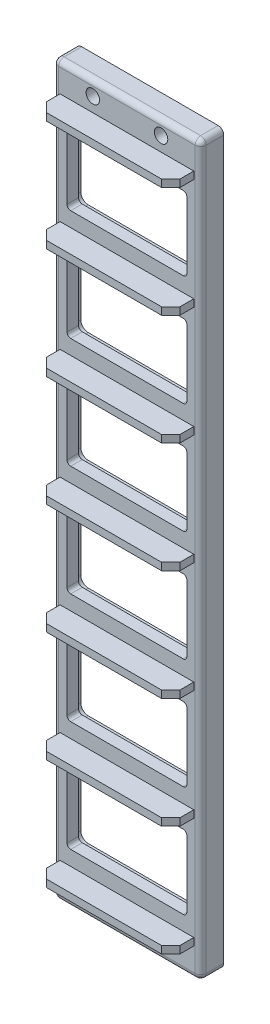
SolidWorks part; units mm, degrees
ref_plane "Front Plane" through (0, 0, 0) normal (0, 0, 1) x (1, 0, 0)
ref_plane "Top Plane" through (0, 0, 0) normal (0, 1, 0) x (1, 0, 0)
ref_plane "Right Plane" through (0, 0, 0) normal (1, 0, 0) x (0, 0, -1)
sketch "Sketch2" plane through (0, 0, 0) normal (0, 0, 1) x (1, 0, 0)
  line L0 (-101.9175, -92.329) -> (-83.5025, -92.329) construction
  line L7 (-101.9175, -107.569) -> (-83.5025, -107.569) construction
  line L14 (-101.9175, -108.077) -> (-83.5025, -108.077)
  line L21 (-101.9175, -107.061) -> (-83.5025, -107.061)
  line L34 (-101.9175, -108.077) -> (-101.9175, -107.061)
  line L35 (-83.5025, -108.077) -> (-83.5025, -107.061)
  arc A0 (-100.6475, -91.059) -> (-100.6475, -93.599) centre (-100.6475, -92.329) ccw construction
  arc A1 (-84.7725, -93.599) -> (-84.7725, -91.059) centre (-84.7725, -92.329) ccw construction
  dimension "D1" = 15.24
  dimension "D4" = 0.508
  dimension "D5" = 0.508
  dimension "D3" = 2
extrude "Boss-Extrude1" add sketch "Sketch2" along normal blind 6.35
chamfer "Chamfer1" distance 1.27 angle 45 2 edges at (-101.9175, -107.569, 6.35) (-83.5025, -107.569, 6.35)
pattern_linear "LPattern2" count 7 spacing 15.24 along (0, 1, 0) of bodies 107
sketch "Sketch3" plane through (0, 0, 0) normal (0, 0, 1) x (1, 0, 0)
  line L0 (-102.87, -112.014) -> (-82.55, -112.014) construction
  line L1 (-82.55, -112.014) -> (-82.55, -11.684) construction
  line L2 (-82.55, -11.684) -> (-102.87, -11.684) construction
  line L3 (-102.87, -11.684) -> (-102.87, -112.014) construction
  line L4 (-84.455, -94.869) -> (-100.965, -94.869) construction
  line L5 (-100.965, -94.869) -> (-100.965, -105.029) construction
  line L6 (-100.965, -105.029) -> (-84.455, -105.029) construction
  line L7 (-84.455, -105.029) -> (-84.455, -94.869) construction
  line L8 (-84.455, -89.789) -> (-84.455, -79.629) construction
  line L9 (-84.455, -79.629) -> (-100.965, -79.629) construction
  line L10 (-100.965, -79.629) -> (-100.965, -89.789) construction
  line L11 (-100.965, -89.789) -> (-84.455, -89.789) construction
  line L12 (-84.455, -74.549) -> (-84.455, -64.389) construction
  line L13 (-84.455, -64.389) -> (-100.965, -64.389) construction
  line L14 (-100.965, -64.389) -> (-100.965, -74.549) construction
  line L15 (-100.965, -74.549) -> (-84.455, -74.549) construction
  line L16 (-84.455, -59.309) -> (-84.455, -49.149) construction
  line L17 (-84.455, -49.149) -> (-100.965, -49.149) construction
  line L18 (-100.965, -49.149) -> (-100.965, -59.309) construction
  line L19 (-100.965, -59.309) -> (-84.455, -59.309) construction
  line L20 (-84.455, -44.069) -> (-84.455, -33.909) construction
  line L21 (-84.455, -33.909) -> (-100.965, -33.909) construction
  line L22 (-100.965, -33.909) -> (-100.965, -44.069) construction
  line L23 (-100.965, -44.069) -> (-84.455, -44.069) construction
  line L24 (-84.455, -28.829) -> (-84.455, -18.669) construction
  line L25 (-84.455, -18.669) -> (-100.965, -18.669) construction
  line L26 (-100.965, -18.669) -> (-100.965, -28.829) construction
  line L27 (-100.965, -28.829) -> (-84.455, -28.829) construction
  line L28 (-102.87, -112.014) -> (-82.55, -112.014)
  line L29 (-82.55, -112.014) -> (-82.55, -11.684)
  line L30 (-82.55, -11.684) -> (-102.87, -11.684)
  line L31 (-102.87, -11.684) -> (-102.87, -112.014)
  line L32 (-84.455, -94.869) -> (-100.965, -94.869)
  line L33 (-100.965, -94.869) -> (-100.965, -105.029)
  line L34 (-100.965, -105.029) -> (-84.455, -105.029)
  line L35 (-84.455, -105.029) -> (-84.455, -94.869)
  line L36 (-84.455, -89.789) -> (-84.455, -79.629)
  line L37 (-84.455, -79.629) -> (-100.965, -79.629)
  line L38 (-100.965, -79.629) -> (-100.965, -89.789)
  line L39 (-100.965, -89.789) -> (-84.455, -89.789)
  line L40 (-84.455, -74.549) -> (-84.455, -64.389)
  line L41 (-84.455, -64.389) -> (-100.965, -64.389)
  line L42 (-100.965, -64.389) -> (-100.965, -74.549)
  line L43 (-100.965, -74.549) -> (-84.455, -74.549)
  line L44 (-84.455, -59.309) -> (-84.455, -49.149)
  line L45 (-84.455, -49.149) -> (-100.965, -49.149)
  line L46 (-100.965, -49.149) -> (-100.965, -59.309)
  line L47 (-100.965, -59.309) -> (-84.455, -59.309)
  line L48 (-84.455, -44.069) -> (-84.455, -33.909)
  line L49 (-84.455, -33.909) -> (-100.965, -33.909)
  line L50 (-100.965, -33.909) -> (-100.965, -44.069)
  line L51 (-100.965, -44.069) -> (-84.455, -44.069)
  line L52 (-84.455, -28.829) -> (-84.455, -18.669)
  line L53 (-84.455, -18.669) -> (-100.965, -18.669)
  line L54 (-100.965, -18.669) -> (-100.965, -28.829)
  line L55 (-100.965, -28.829) -> (-84.455, -28.829)
extrude "Boss-Extrude2" add sketch "Sketch3" along normal blind 3.175
fillet "Fillet1" radius 0.762 8 edges at (-102.87, -112.014, 1.5875) (-92.71, -112.014, 3.175) (-82.55, -112.014, 1.5875) (-92.71, -11.684, 3.175) (-102.87, -61.849, 3.175) (-82.55, -61.849, 3.175) (-102.87, -11.684, 1.5875) (-82.55, -11.684, 1.5875)
hole_wizard "#0 Clearance Hole1" positions "Sketch8" profile "Sketch7" hole size "#0" standard "ANSI Inch" end condition through all
sketch "Sketch8" plane through (0, 0, 3.175) normal (0, 0, 1) x (1, 0, 0)
  line L0 (-92.71, -15.621) -> (-92.71, -11.684) construction
  line L1 (-101.9175, -15.621) -> (-83.5025, -15.621) construction
  line L2 (-102.108, -11.684) -> (-83.312, -11.684) construction
  line L4 (-92.71, -13.6525) -> (-102.108, -13.6525) construction
  line L5 (-102.108, -12.446) -> (-102.108, -111.252) construction
  line L6 (-102.87, -61.849) -> (-82.55, -61.849) construction
  line L7 (-102.87, -111.252) -> (-102.87, -12.446) construction
  line L8 (-82.55, -12.446) -> (-82.55, -111.252) construction
  point P19 (-97.409, -13.6525)
  point P21 (-88.011, -13.6525)
  point P30 (-97.409, -110.0455)
  point P31 (-88.011, -110.0455)
sketch "Sketch7" plane through (-97.409, -13.6525, 3.175) normal (1, 0, 0) x (0, -1, 0)
  line L0 (0, 0) -> (0, 3.175)
  line L1 (0, 3.175) -> (0.9271, 3.175)
  line L2 (0.9271, 3.175) -> (0.9271, 0)
  line L5 (0.9271, 0) -> (0, 0)
  line L11 (0, -6.35) -> (0, 107.95) construction
  dimension "Thru Hole Dia." = 1.8542
  dimension "Thru Hole Depth" = 3.175
fillet "Fillet2" radius 0.508 24 edges at (-100.965, -28.829, 1.5875) (-100.965, -18.669, 1.5875) (-84.455, -18.669, 1.5875) (-84.455, -28.829, 1.5875) (-100.965, -59.309, 1.5875) (-100.965, -49.149, 1.5875) (-84.455, -49.149, 1.5875) (-84.455, -59.309, 1.5875) (-100.965, -89.789, 1.5875) (-100.965, -79.629, 1.5875) (-84.455, -79.629, 1.5875) (-84.455, -89.789, 1.5875) (-100.965, -94.869, 1.5875) (-84.455, -94.869, 1.5875) (-100.965, -74.549, 1.5875) (-100.965, -64.389, 1.5875) (-84.455, -64.389, 1.5875) (-84.455, -74.549, 1.5875) (-100.965, -44.069, 1.5875) (-100.965, -33.909, 1.5875) (-84.455, -33.909, 1.5875) (-84.455, -44.069, 1.5875) (-100.965, -105.029, 1.5875) (-84.455, -105.029, 1.5875)
sketch "Sketch9" plane through (0, 0, 0) normal (0, 0, -1) x (-1, 0, 0)
  line L0 (102.235, -105.283) -> (102.235, -94.615)
  line L1 (101.219, -93.599) -> (84.201, -93.599)
  line L2 (83.185, -94.615) -> (83.185, -105.283)
  line L3 (84.201, -106.299) -> (101.219, -106.299)
  line L4 (101.727, -105.283) -> (101.727, -94.615)
  line L5 (101.219, -94.107) -> (84.201, -94.107)
  line L6 (83.693, -94.615) -> (83.693, -105.283)
  line L7 (84.201, -105.791) -> (101.219, -105.791)
  line L8 (101.727, -105.283) -> (101.727, -94.615) construction
  line L9 (101.219, -94.107) -> (84.201, -94.107) construction
  line L10 (83.693, -94.615) -> (83.693, -105.283) construction
  line L11 (84.201, -105.791) -> (101.219, -105.791) construction
  arc A0 (102.235, -94.615) -> (101.219, -93.599) centre (101.219, -94.615) ccw
  arc A1 (84.201, -93.599) -> (83.185, -94.615) centre (84.201, -94.615) ccw
  arc A2 (83.185, -105.283) -> (84.201, -106.299) centre (84.201, -105.283) ccw
  arc A3 (101.219, -106.299) -> (102.235, -105.283) centre (101.219, -105.283) ccw
  arc A4 (101.727, -94.615) -> (101.219, -94.107) centre (101.219, -94.615) ccw
  arc A5 (84.201, -94.107) -> (83.693, -94.615) centre (84.201, -94.615) ccw
  arc A6 (83.693, -105.283) -> (84.201, -105.791) centre (84.201, -105.283) ccw
  arc A7 (101.219, -105.791) -> (101.727, -105.283) centre (101.219, -105.283) ccw
  arc A8 (101.727, -94.615) -> (101.219, -94.107) centre (101.219, -94.615) ccw construction
  arc A9 (84.201, -94.107) -> (83.693, -94.615) centre (84.201, -94.615) ccw construction
  arc A10 (83.693, -105.283) -> (84.201, -105.791) centre (84.201, -105.283) ccw construction
  arc A11 (101.219, -105.791) -> (101.727, -105.283) centre (101.219, -105.283) ccw construction
  dimension "D1" = 0
  dimension "D2" = 0.508
extrude "Cut-Extrude1" cut sketch "Sketch9" against normal blind 1.5875
pattern_linear "LPattern3" count 6 spacing 15.24 along (0, 1, 0) of "Cut-Extrude1"
